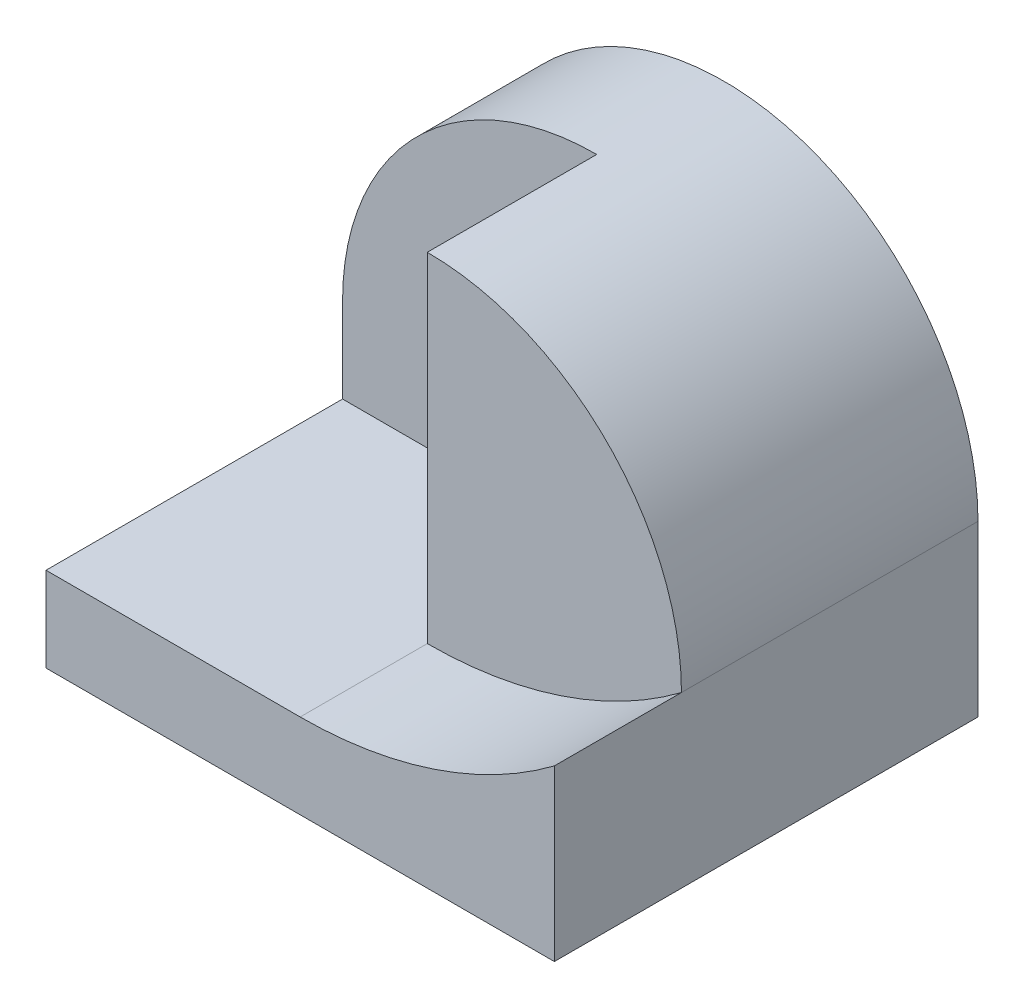
SolidWorks part; units mm, degrees
ref_plane "Front Plane" through (0, 0, 0) normal (0, 0, 1) x (1, 0, 0)
ref_plane "Top Plane" through (0, 0, 0) normal (0, 1, 0) x (1, 0, 0)
ref_plane "Right Plane" through (0, 0, 0) normal (1, 0, 0) x (0, 0, -1)
sketch "Sketch2" plane through (0, 0, 0) normal (0, 0, 1) x (1, 0, 0)
  line L1 (0, 0) -> (60, 0)
  line L2 (0, 0) -> (0, 10)
  line L3 (0, 10) -> (60, 10)
  line L4 (60, 0) -> (60, 10)
  dimension "D1" = 60
  dimension "D2" = 10
extrude "Boss-Extrude10" add sketch "Sketch2" along normal blind 50
sketch "Sketch9" plane through (0, 0, 0) normal (0, 0, -1) x (-1, 0, 0)
  line L0 (-60, 10) -> (0, 10) construction
  line L1 (-30, 50) -> (-30, 20)
  line L2 (-30, 20) -> (0, 20)
  arc A0 (0, 20) -> (-30, 50) centre (-30, 20) ccw
  point P3 (-30, 10)
  dimension "D1" = 30
  dimension "D2" = 10
  dimension "D3" = 40
  dimension "D4" = 30
  dimension "D5" = 30
extrude "Boss-Extrude11" add sketch "Sketch9" against normal blind 15 separate body
sketch "Sketch10" plane through (0, 0, 0) normal (0, 0, -1) x (-1, 0, 0)
  line L0 (-60, 20) -> (-30, 20)
  line L1 (-30, 20) -> (-30, 50)
  arc A0 (-60, 20) -> (-30, 50) centre (-30, 20) cw
  dimension "D1" = 30
  dimension "D2" = 10
  dimension "D3" = 30
extrude "Boss-Extrude12" add sketch "Sketch10" against normal blind 35
sketch "Sketch12" plane through (0, 0, 50) normal (0, 0, 1) x (1, 0, 0)
  line L0 (60, 10) -> (60, 20)
  line L1 (60, 10) -> (0, 10) construction
  line L2 (30, 10) -> (60, 10)
  line L3 (0, 10) -> (0, 20)
  line L4 (0, 20) -> (60, 20)
  line L5 (0, 10) -> (30, 10)
  arc A0 (30, 10) -> (60, 20) centre (30, 60) ccw
  line M4 (60, 10) -> (0, 10)
  dimension "D1" = 10
extrude "Boss-Extrude14" add sketch "Sketch12" against normal blind 50 contours A0 L0 M4
sketch "Sketch13" plane through (0, 0, 0) normal (0, 0, -1) x (-1, 0, 0)
  line L0 (0, 20) -> (-60, 20)
  line L1 (0, 20) -> (0, 10)
  line L2 (0, 10) -> (-30, 10)
  arc A0 (-60, 20) -> (-30, 10) centre (-30, 60) ccw
extrude "Boss-Extrude18" add sketch "Sketch13" against normal blind 35
sketch "Sketch14" plane through (0, 0, 35) normal (0, 0, 1) x (1, 0, 0)
  line L1 (0, 20) -> (30, 20)
  line L2 (0, 20) -> (0, 10)
  line L3 (0, 10) -> (30, 10)
  line L4 (30, 20) -> (30, 10)
extrude "Cut-Extrude1" cut sketch "Sketch14" against normal blind 20
